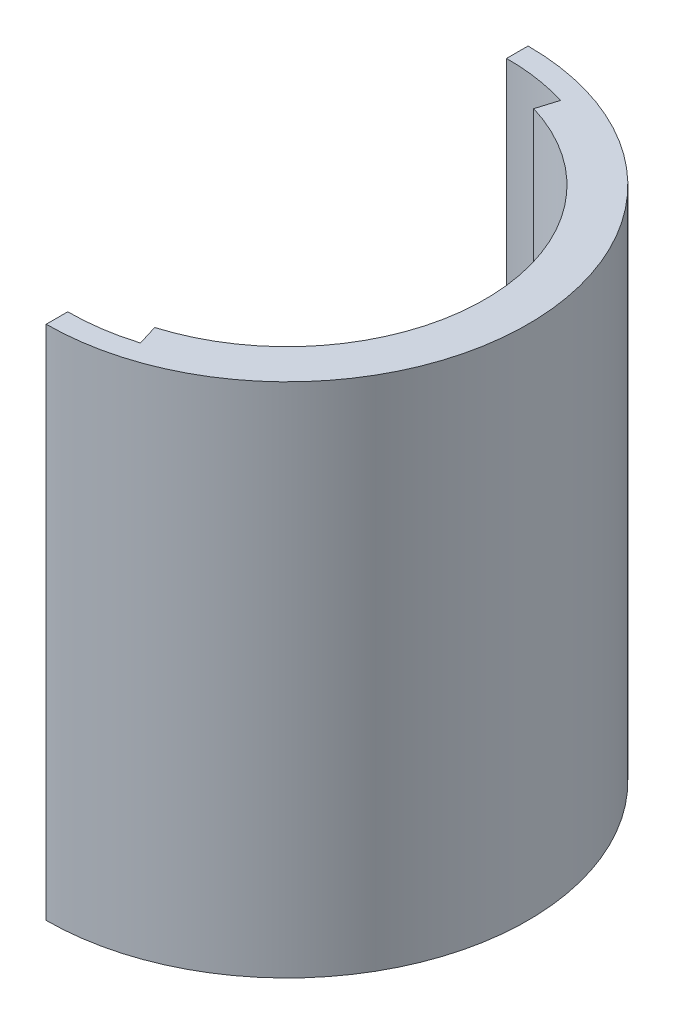
SolidWorks part; units mm, degrees
ref_plane "Front Plane" through (0, 0, 0) normal (0, 0, 1) x (1, 0, 0)
ref_plane "Top Plane" through (0, 0, 0) normal (0, 1, 0) x (1, 0, 0)
ref_plane "Right Plane" through (0, 0, 0) normal (1, 0, 0) x (0, 0, -1)
sketch "Sketch2" plane through (0, 0, 0) normal (0, 1, 0) x (1, 0, 0)
  circle A0 centre (0, 0) radius 28
  dimension "D1" = 56
extrude "Boss-Extrude1" add sketch "Sketch2" along normal blind 60
sketch "Sketch3" plane through (0, 0, 0) normal (0, -1, 0) x (1, 0, 0)
  circle A0 centre (0, 0) radius 23
  dimension "D1" = 46
extrude "Cut-Extrude2" cut sketch "Sketch3" against normal through all contours A0
sketch "Sketch4" plane through (0, 0, 0) normal (0, -1, 0) x (1, 0, 0)
  line L0 (0, 28) -> (0, 25.5)
  line L1 (7.366, 24.413) -> (6.634, 22.0225)
  line L2 (6.634, -22.0225) -> (7.366, -24.4129)
  line L3 (0, -28) -> (0, -25.5)
  circle A0 centre (0, 0) radius 28 construction
  arc A1 (0, 25.5) -> (7.366, 24.413) centre (0, 0) cw
  circle A2 centre (0, 0) radius 23 construction
  arc A3 (6.634, 22.0225) -> (6.634, -22.0225) centre (-0.1094, 0) cw
  arc A4 (0, 28) -> (0, -28) centre (0, 0) cw
  arc A5 (0, -25.5) -> (7.366, -24.4129) centre (0, -0.0005) ccw
  point P7 (0, 26.75)
  point P8 (7, 23.2177)
  dimension "D2" = 25.5
  dimension "D1" = 2.5
  dimension "D3" = 2.5
  dimension "D4" = 7
  dimension "D5" = 2.5
  dimension "D6" = 2.5
sketch "Sketch5" plane through (0, 0, 0) normal (0, -1, 0) x (1, 0, 0)
  line L0 (0, 28) -> (0, 25.5)
  line L1 (7.366, 24.413) -> (6.634, 22.0225)
  line L2 (6.634, -22.0225) -> (7.366, -24.4129)
  line L3 (0, -25.5) -> (0, -28)
  arc A0 (0, 25.5) -> (7.366, 24.413) centre (0, 0) cw
  arc A1 (6.634, 22.0225) -> (6.634, -22.0225) centre (-0.1094, 0) ccw
  arc A2 (7.366, -24.4129) -> (0, -25.5) centre (0.1016, -0.689) cw
  arc A3 (0, -28) -> (0, 28) centre (0, 0) cw
extrude "Cut-Extrude3" cut sketch "Sketch5" against normal through all
